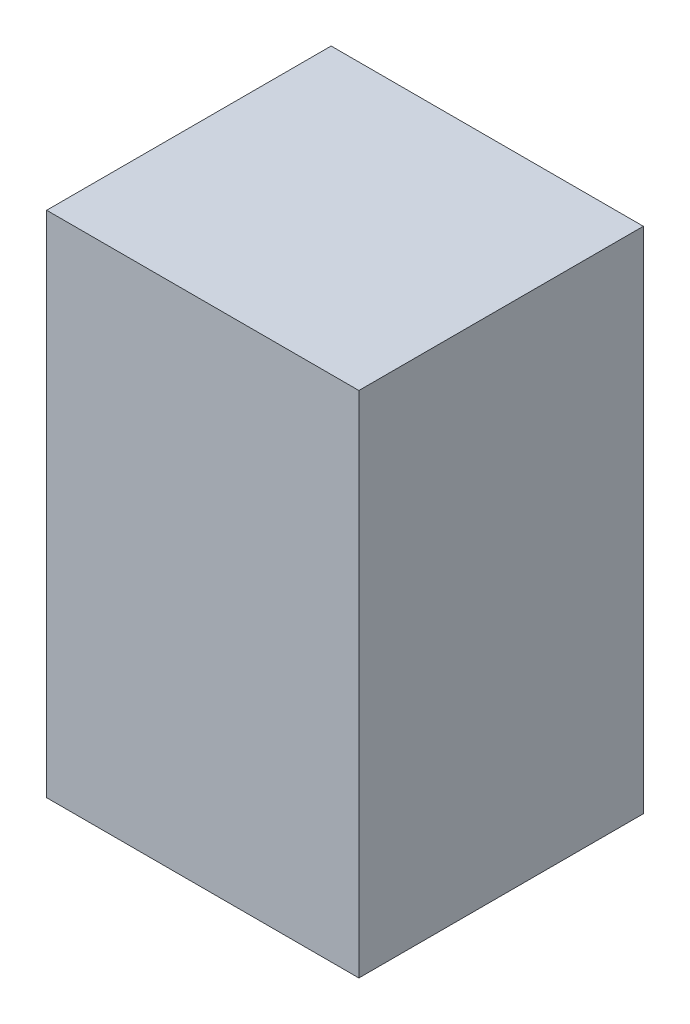
SolidWorks part; units mm, degrees
ref_plane "前视基准面" through (0, 0, 0) normal (0, 0, 1) x (1, 0, 0)
ref_plane "上视基准面" through (0, 0, 0) normal (0, 1, 0) x (1, 0, 0)
ref_plane "右视基准面" through (0, 0, 0) normal (1, 0, 0) x (0, 0, -1)
sketch "草图1" plane through (0, 0, 0) normal (0, 0, 1) x (1, 0, 0)
  line L1 (-135, -220) -> (135, -220)
  line L2 (-135, -220) -> (-135, 220)
  line L3 (-135, 220) -> (135, 220)
  line L4 (135, -220) -> (135, 220)
  line L5 (-135, -220) -> (135, 220) construction
  line L6 (-135, 220) -> (135, -220) construction
  point P0 (0, 0)
extrude "拉伸1" add sketch "草图1" along normal blind 246
